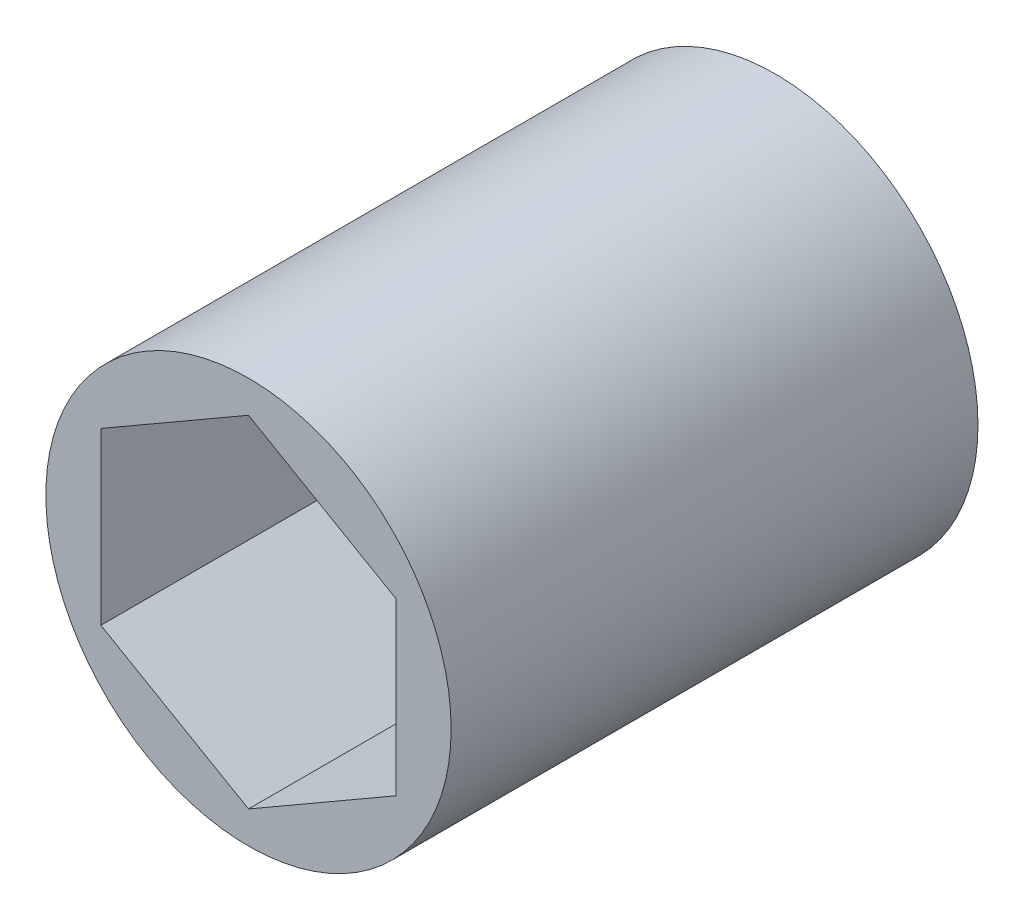
SolidWorks part; units mm, degrees
material "PET"
ref_plane "Front" through (0, 0, 0) normal (0, 0, 1) x (1, 0, 0)
ref_plane "Top" through (0, 0, 0) normal (0, 1, 0) x (1, 0, 0)
ref_plane "Right" through (0, 0, 0) normal (1, 0, 0) x (0, 0, -1)
sketch "Sketch1" plane through (0, 0, 0) normal (0, 0, 1) x (1, 0, 0)
  line L1 (0, 7.479) -> (-6.477, 3.7395)
  line L2 (-6.477, 3.7395) -> (-6.477, -3.7395)
  line L3 (-6.477, -3.7395) -> (0, -7.479)
  line L4 (0, -7.479) -> (6.477, -3.7395)
  line L5 (6.477, -3.7395) -> (6.477, 3.7395)
  line L6 (6.477, 3.7395) -> (0, 7.479)
  circle A0 centre (0, 0) radius 8.89
  circle A1 centre (0, 0) radius 6.477 construction
  dimension "D2" = 17.78
  dimension "D1" = 12.954
extrude "Boss-Extrude1" add sketch "Sketch1" along normal blind 23.114
